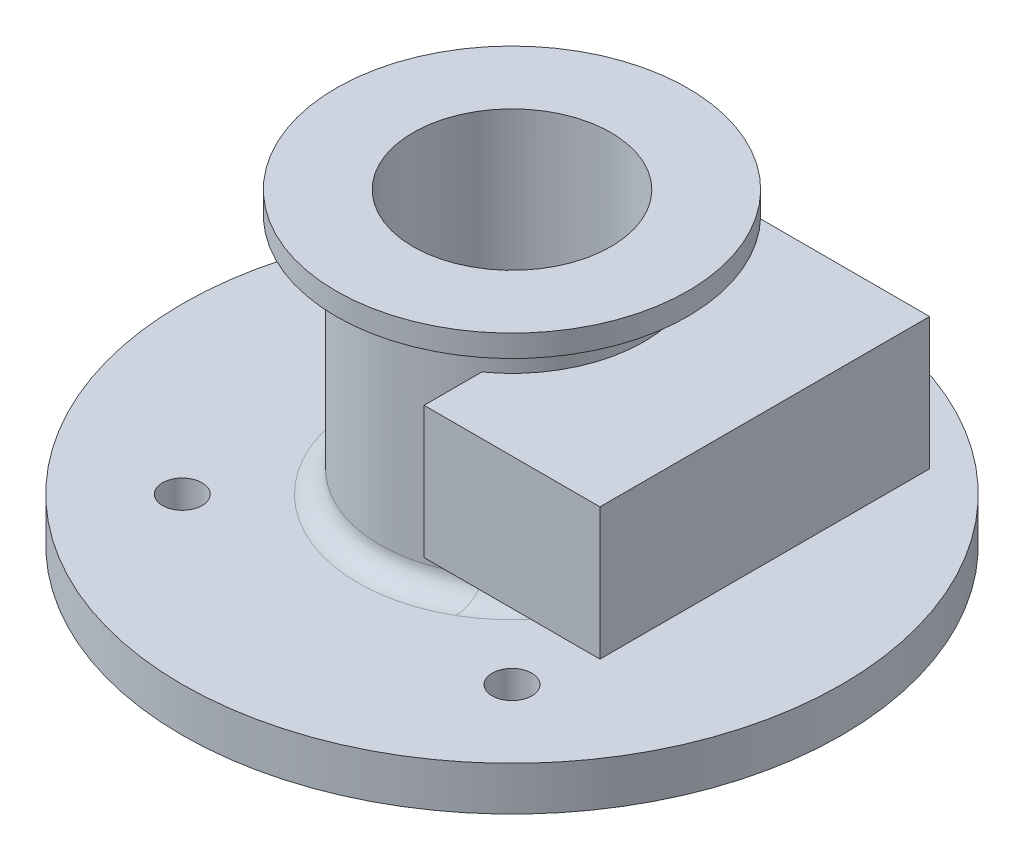
SolidWorks part; units mm, degrees
ref_plane "Front Plane" through (0, 0, 0) normal (0, 0, 1) x (1, 0, 0)
ref_plane "Top Plane" through (0, 0, 0) normal (0, 1, 0) x (1, 0, 0)
ref_plane "Right Plane" through (0, 0, 0) normal (1, 0, 0) x (0, 0, -1)
sketch "Sketch1" plane through (0, 0, 0) normal (0, 1, 0) x (1, 0, 0)
  circle A0 centre (0, 0) radius 75
  circle A1 centre (37.5, 37.5) radius 4.5
  circle A2 centre (-37.5, 37.5) radius 4.5
  circle A3 centre (-37.5, -37.5) radius 4.5
  circle A4 centre (37.5, -37.5) radius 4.5
  point P16 (0, 0)
  dimension "D1" = 150
  dimension "D4" = 9
  dimension "D5" = 4
extrude "Boss-Extrude1" add sketch "Sketch1" along normal blind 10
sketch "Sketch2" plane through (0, 10, 0) normal (0, 1, 0) x (1, 0, 0)
  circle A0 centre (0, 0) radius 30
  dimension "D1" = 60
extrude "Boss-Extrude2" add sketch "Sketch2" along normal blind 55
sketch "Sketch3" plane through (0, 65, 0) normal (0, 1, 0) x (1, 0, 0)
  circle A0 centre (0, 0) radius 40
  dimension "D1" = 80
extrude "Boss-Extrude3" add sketch "Sketch3" along normal blind 5
sketch "Sketch4" plane through (0, 70, 0) normal (0, 1, 0) x (1, 0, 0)
  circle A0 centre (0, 0) radius 22.5
  dimension "D1" = 45
extrude "Cut-Extrude1" cut sketch "Sketch4" against normal blind 60
fillet "Fillet1" radius 5 2 edges at (0, 10, 30) (0, 65, 30)
sketch "Sketch5" plane through (0, 10, 0) normal (0, 1, 0) x (1, 0, 0)
  line L1 (17.5, 37.5) -> (57.5, 37.5)
  line L2 (57.5, 37.5) -> (57.5, -37.5)
  line L3 (57.5, -37.5) -> (17.5, -37.5)
  line L4 (17.5, 37.5) -> (17.5, -37.5)
extrude "Boss-Extrude4" add sketch "Sketch5" along normal blind 45
sketch "Sketch6" plane through (0, 0, 37.5) normal (0, 0, 1) x (1, 0, 0)
  line L0 (30, 55) -> (30, 25)
  line L1 (30, 25) -> (57.5, 25)
  line L2 (57.5, 55) -> (57.5, 10) construction
  line L3 (57.5, 25) -> (57.5, 55)
  line L4 (57.5, 55) -> (30, 55)
  line L5 (57.5, 25) -> (57.5, 10)
  line L6 (57.5, 10) -> (17.5, 10)
  line L7 (17.5, 10) -> (17.5, 25)
  line L8 (17.5, 55) -> (17.5, 10) construction
  line L9 (17.5, 25) -> (30, 25)
  line M2 (17.5, 10) -> (33, 10)
  line M3 (33, 10) -> (42, 10)
  line M4 (42, 10) -> (57.5, 10)
  line M5 (57.5, 10) -> (57.5, 55)
  line M7 (17.5, 55) -> (17.5, 10)
  dimension "D1" = 30
extrude "Cut-Extrude2" cut sketch "Sketch6" against normal through all contours L9 L1 M7 M2 M3 M4 M5
sketch "Sketch7" plane through (0, 10, 0) normal (0, 1, 0) x (1, 0, 0)
  circle A0 centre (0, 0) radius 30
  dimension "D1" = 60
extrude "Boss-Extrude5" add sketch "Sketch7" along normal up to surface (15 mm away) up to face at (27.5, 25, 0)
fillet "Fillet2" radius 5 1 edges at (30, 10, 0)
sketch "Sketch8" plane through (0, 70, 0) normal (0, 1, 0) x (1, 0, 0)
  arc A0 (17.5, 14.1421) -> (17.5, -14.1421) centre (0, 0) ccw construction
  arc A1 (17.5, 14.1421) -> (17.5, -14.1421) centre (0, 0) ccw
  arc A2 (17.5, -14.1421) -> (17.5, 14.1421) centre (0, 0) ccw construction
  arc A3 (17.5, -14.1421) -> (17.5, 14.1421) centre (0, 0) ccw
extrude "Cut-Extrude3" cut sketch "Sketch8" against normal blind 45
